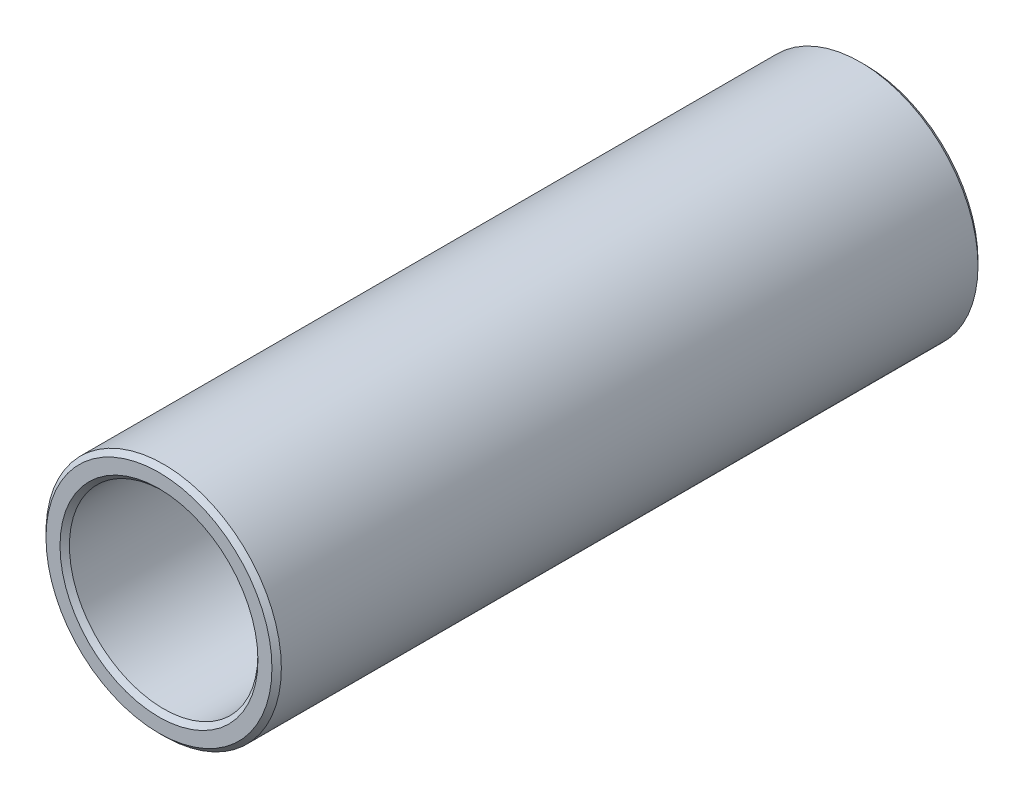
SolidWorks part; units mm, degrees
material "1.4307 (X2CrNi18-9)"
ref_plane "Plan de face" through (0, 0, 0) normal (0, 0, 1) x (1, 0, 0)
ref_plane "Plan de dessus" through (0, 0, 0) normal (0, 1, 0) x (1, 0, 0)
ref_plane "Plan de droite" through (0, 0, 0) normal (1, 0, 0) x (0, 0, -1)
sketch "Esquisse1" plane through (0, 0, 0) normal (0, 0, 1) x (1, 0, 0)
  circle A0 centre (0, 0) radius 4.005
  circle A1 centre (0, 0) radius 5
  dimension "D1" = 8.01
  dimension "D2" = 10
extrude "Boss.-Extru.1" add sketch "Esquisse1" along normal blind 30
chamfer "Chanfrein1" distance 0.2 angle 45 4 edges at (5, 0, 0) (5, 0, 30) (4.005, 0, 0) (4.005, 0, 30)
